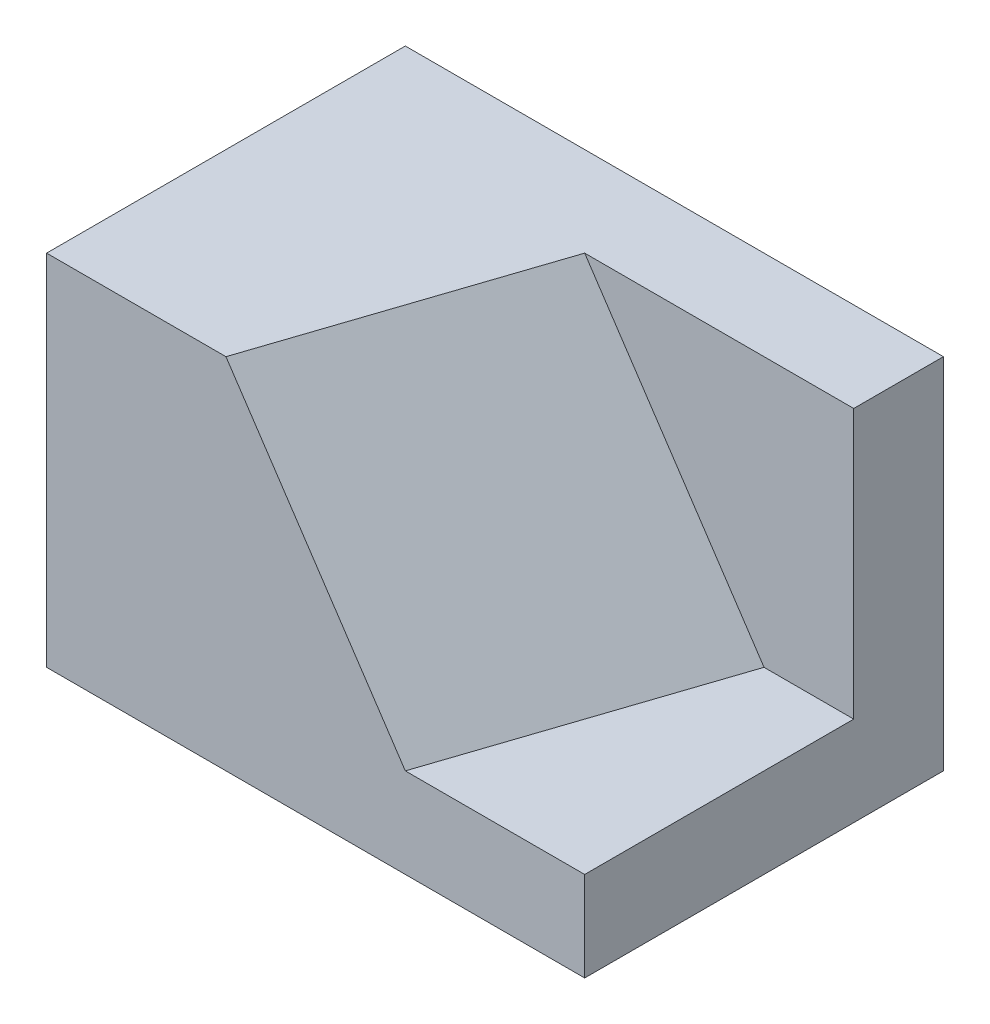
SolidWorks part; units mm, degrees
ref_plane "前基準面" through (0, 0, 0) normal (0, 0, 1) x (1, 0, 0)
ref_plane "上基準面" through (0, 0, 0) normal (0, 1, 0) x (1, 0, 0)
ref_plane "右基準面" through (0, 0, 0) normal (1, 0, 0) x (0, 0, -1)
sketch "草圖1" plane through (0, 0, 0) normal (0, 1, 0) x (1, 0, 0)
  line L1 (15, 10) -> (-15, 10)
  line L2 (15, 10) -> (15, -10)
  line L3 (15, -10) -> (-15, -10)
  line L4 (-15, 10) -> (-15, -10)
  line L5 (15, 10) -> (-15, -10) construction
  line L6 (15, -10) -> (-15, 10) construction
  point P0 (0, 0)
  dimension "D1" = 20
  dimension "D2" = 30
extrude "填料-伸長1" add sketch "草圖1" along normal blind 20
sketch "草圖2" plane through (0, 0, 10) normal (0, 0, 1) x (1, 0, 0)
  line L0 (-5, 20) -> (5, 5)
  line L1 (5, 5) -> (15, 5)
  line L2 (15, 20) -> (15, 0) construction
  line L3 (15, 5) -> (10, 5)
  line L4 (10, 5) -> (0, 20)
  line L5 (-15, 20) -> (15, 20) construction
  line L6 (-15, 0) -> (15, 0) construction
  dimension "D1" = 5
  dimension "D2" = 10
  dimension "D3" = 5
  dimension "D4" = 15
  dimension "D5" = 5
sketch "草圖3" plane through (0, 20, 0) normal (0, 1, 0) x (1, 0, 0)
  line L0 (-5, -10) -> (0, 5)
  line L1 (-5, -10) -> (5, -10) construction
  line L2 (-15, -10) -> (15, -10) construction
  line L3 (0, 5) -> (15, 5)
  line L4 (15, -10) -> (15, 10) construction
  line L5 (15, 5) -> (10, 5)
  line L6 (10, 5) -> (5, -10)
  line L7 (15, 10) -> (-15, 10) construction
  dimension "D1" = 5
  dimension "D2" = 5
  dimension "D3" = 10
  dimension "D4" = 10
  dimension "D5" = 10
ref_plane "平面1" through (7.5, 5, 2.5) normal (-0.8018, -0.5345, -0.2673) x (-0.2224, -0.1482, 0.9636)
sketch "草圖6" plane through (7.5, 5, 2.5) normal (-0.8018, -0.5345, -0.2673) x (-0.2224, -0.1482, 0.9636)
  line L2 (7.7831, 19.4145) -> (7.7831, 1.3868) construction
  line L5 (7.7831, 19.4145) -> (-7.7831, 16.641) construction
  line L8 (7.7831, 19.4145) -> (7.7831, 1.3868)
  line L11 (7.7831, 19.4145) -> (-7.7831, 16.641)
  line L14 (7.7831, 1.3868) -> (-7.7831, 1.3868)
  line L15 (-7.7831, 1.3868) -> (-7.7831, 16.641)
sketch "草圖5" plane through (15, 0, 0) normal (1, 0, 0) x (0, 0, -1)
  line L0 (5, 20) -> (5, 5)
  line L1 (5, 20) -> (-10, 20) construction
  line L2 (-10, 20) -> (10, 20) construction
  line L3 (5, 5) -> (-10, 5)
  line L4 (-10, 5) -> (-10, 20) construction
  line L5 (-10, 0) -> (10, 0) construction
  line L6 (10, 20) -> (10, 0) construction
  line L7 (-10, 5) -> (-10, 20)
  line L8 (-10, 20) -> (-10, 5) construction
  line L9 (-10, 20) -> (5, 20) construction
  line L10 (-10, 20) -> (5, 20)
  dimension "D1" = 360
  dimension "D2" = 5
extrude "除料-伸長3" cut sketch "草圖5" against normal up to surface (20 mm away) up to plane "平面1"
scale "縮放比例1" scale about centroid uniform scaling yes scale factor 0.2
